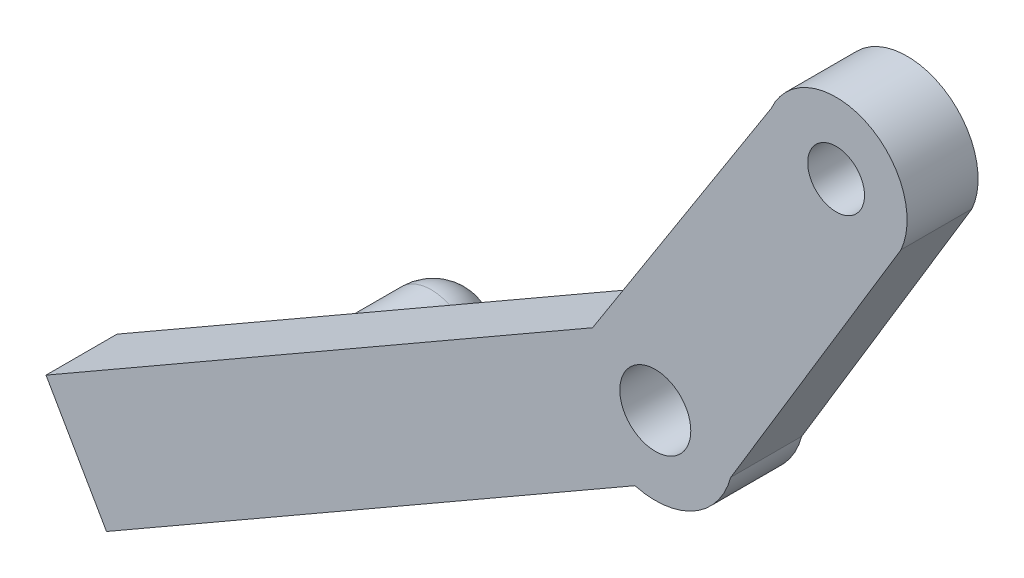
SolidWorks part; units mm, degrees
ref_plane "Front Plane" through (0, 0, 0) normal (0, 0, 1) x (1, 0, 0)
ref_plane "Top Plane" through (0, 0, 0) normal (0, 1, 0) x (1, 0, 0)
ref_plane "Right Plane" through (0, 0, 0) normal (1, 0, 0) x (0, 0, -1)
sketch "Sketch1" plane through (0, 0, 0) normal (0, 0, 1) x (0.4985, -0.8669, 0)
  line L0 (4.6263, -46.838) -> (4.6263, -41.838) construction
  line L2 (8.8991, 3.8691) -> (-2.3564, 24.18)
  line L3 (1.121, -3.909) -> (-10.421, 18.2671)
  line L4 (-2.3564, 24.18) -> (-10.421, 18.2671) construction
  line L6 (0.3536, -46.838) -> (8.8991, -46.838)
  line L7 (0.3536, -46.838) -> (0.3536, -2.4346)
  line L9 (8.8991, -46.838) -> (8.8991, -3.909)
  circle A0 centre (5.01, -0.02) radius 2.5
  arc A1 (1.121, -3.909) -> (8.8991, 3.8691) centre (5.01, -0.02) ccw
  arc A2 (-2.3564, 24.18) -> (-10.421, 18.2671) centre (-6.3887, 21.2235) ccw
  circle A3 centre (-6.3887, 21.2235) radius 2
  circle A5 centre (5.01, -0.02) radius 5.5 construction
  point P16 (10.01, -0.02)
  dimension "D2" = 4
  dimension "D3" = 5
  dimension "D5" = 5
  dimension "D4" = 25
  dimension "D6" = 42.929
  dimension "D7" = 8.5456
  dimension "D8" = 10
  dimension "D1" = 3
extrude "Boss-Extrude1" add sketch "Sketch1" along normal blind 5 contours L2 A2 L3 A1 A3 A0 | A1 L3 L7 L6 L9
sketch "Sketch8" plane through (0, 0, 0) normal (0, 0, -1) x (-1, 0, 0)
  line L0 (38.2963, -27.3606) -> (25.2932, -19.8826) construction
  line L1 (23.2692, -23.6476) -> (36.1662, -31.0645) construction
  line L2 (25.3993, -19.9436) -> (23.2692, -23.6476) construction
  line L3 (38.2963, -27.3606) -> (36.1662, -31.0645) construction
  circle A0 centre (25.2932, -19.8826) radius 3
  dimension "D1" = 6
  dimension "D3" = 4.2728
  dimension "D2" = 15
  dimension "D4" = 14.8776
extrude "Boss-Extrude3" add sketch "Sketch8" along normal blind 10
ref_plane "Plane1" through (2.3064, -4.0104, 0) normal (0.4985, -0.8669, 0) x (-0.8669, -0.4985, 0)
sketch "Sketch9" plane through (2.3064, -4.0104, 0) normal (0.4985, -0.8669, 0) x (-0.8669, -0.4985, 0)
  line L0 (31.838, 10) -> (31.838, 7) construction
  line L1 (34.838, 10) -> (28.838, 10) construction
  line L2 (31.838, 7) -> (34.838, 7) construction
  line L3 (31.838, 10) -> (32.838, 10) construction
  line L4 (32.838, 10) -> (34.838, 10)
  line L5 (34.838, 10) -> (34.838, 7)
  line L6 (34.838, 7.6139) -> (31.838, 7.6139) construction
  arc A0 (34.838, 7) -> (32.838, 10) centre (31.588, 7) ccw
  dimension "D3" = 3
  dimension "D1" = 2
  dimension "D2" = 3
revolve "Cut-Revolve1" cut sketch "Sketch9" angle 360 about L0
sketch "Sketch3" plane through (0, 0, 0) normal (0, 0, -1) x (-1, 0, 0)
  line L0 (36.092, -21.164) -> (18.7546, -11.1934) construction
  line L1 (36.1662, -31.0645) -> (40.4264, -23.6566) construction
  line L2 (40.4264, -23.6566) -> (18.7546, -11.1934) construction
  line L3 (40.4264, -23.6566) -> (1.9342, -1.5202) construction
  line L4 (18.7546, -11.1934) -> (14.4943, -18.6013) construction
  line L5 (36.1662, -31.0645) -> (-1.0478, -9.6632) construction
  line L6 (14.4943, -18.6013) -> (36.1662, -31.0645) construction
  line L7 (36.1662, -31.0645) -> (40.4264, -23.6566)
  line L8 (36.1662, -31.0645) -> (31.8318, -28.5719)
  line L9 (40.4264, -23.6566) -> (36.092, -21.164)
  line L10 (31.8318, -28.5719) -> (36.092, -21.164)
  line L11 (14.4943, -18.6013) -> (18.7546, -11.1934)
  line L12 (14.4943, -18.6013) -> (10.16, -16.1087)
  line L13 (18.7546, -11.1934) -> (14.4202, -8.7007)
  line L14 (10.16, -16.1087) -> (14.4202, -8.7007)
  dimension "D1" = 20
  dimension "D2" = 5
  dimension "D3" = 5
